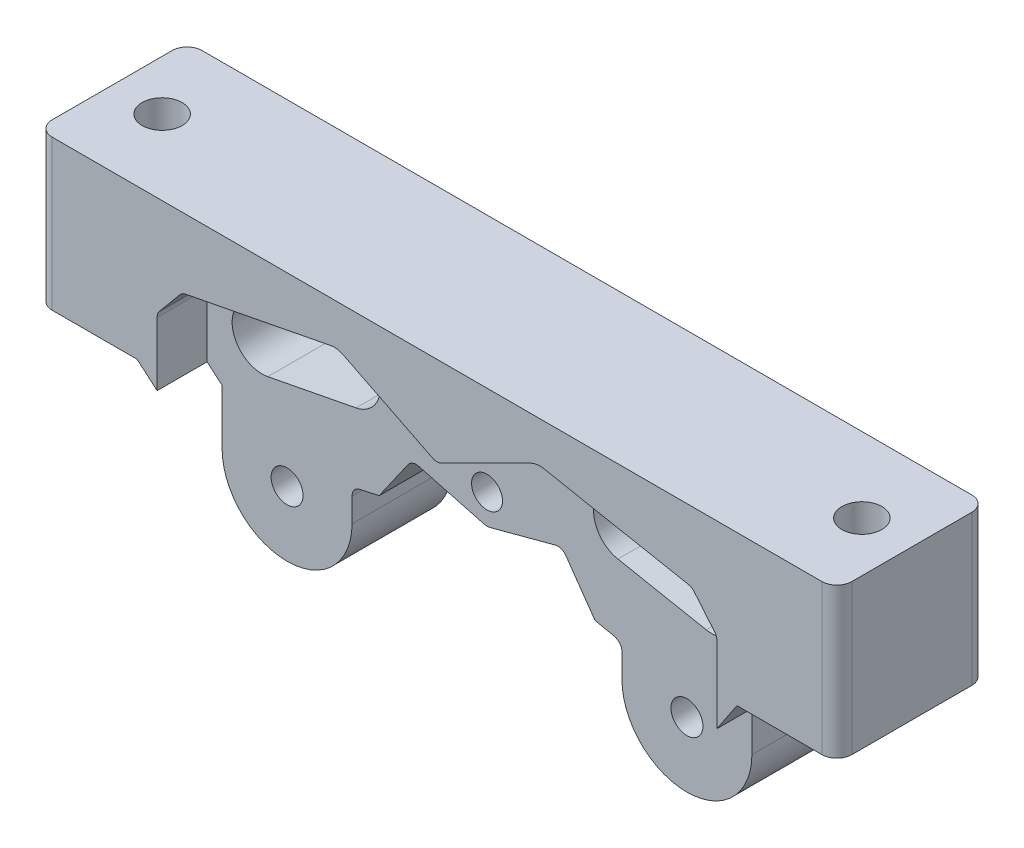
SolidWorks part; units mm, degrees
ref_plane "Front Plane" through (0, 0, 0) normal (0, 0, 1) x (1, 0, 0)
ref_plane "Top Plane" through (0, 0, 0) normal (0, 1, 0) x (1, 0, 0)
ref_plane "Right Plane" through (0, 0, 0) normal (1, 0, 0) x (0, 0, -1)
sketch "Sketch1" plane through (0, 0, 0) normal (0, 0, 1) x (1, 0, 0)
  line L0 (78, 15) -> (78, 0) construction
  line L1 (0, 0) -> (48, 0)
  line L2 (0, 0) -> (0, 15)
  line L3 (0, 15) -> (156, 15)
  line L4 (156, 0) -> (156, 15)
  line L5 (78, 0) -> (78, -15) construction
  line L6 (108, 0) -> (156, 0)
  line L8 (48, 0) -> (48, -15)
  line L9 (48, -15) -> (108, -15)
  line L10 (108, 0) -> (108, -15)
  point P13 (78, -15)
  dimension "D1" = 156
  dimension "D2" = 15
  dimension "D3" = 30
  dimension "D4" = 60
extrude "Boss-Extrude1" add sketch "Sketch1" along normal blind 15
sketch "Sketch2" plane through (0, 0, 15) normal (0, 0, 1) x (1, 0, 0)
  line L0 (78, -15) -> (78, 15) construction
  line L1 (48, -15) -> (108, -15) construction
  line L2 (156, 15) -> (0, 15) construction
  line L3 (85.5, -2) -> (70.5, -2) construction
  line L4 (0, 15) -> (0, 0) construction
  line L5 (0, 7.5) -> (156, 7.5) construction
  line L6 (156, 0) -> (156, 15) construction
  line L7 (89, -5) -> (67, -5) construction
  line L8 (108, 0) -> (48, 0) construction
  line L9 (67.633, 6) -> (88.367, 6) construction
  line L10 (108, -15) -> (108, 0) construction
  line L11 (108, -7.5) -> (48, -7.5) construction
  line L12 (48, 0) -> (48, -15) construction
  line L13 (68, 11) -> (88, 11) construction
  line L14 (77.5528, 6.2236) -> (68.6076, 10.6962)
  line L15 (78.4472, 6.2236) -> (87.3924, 10.6962)
  line L16 (50, 5) -> (106, 5) construction
  line L17 (52.5, 8) -> (103.5, 8) construction
  line L18 (88.6669, 10.8709) -> (103.15, 8.0677)
  line L20 (52.85, 8.0677) -> (67.3331, 10.8709)
  line L21 (105.7682, 5.2781) -> (103.7282, 7.7261)
  line L22 (52.2718, 7.7261) -> (50.2318, 5.2781)
  line L23 (50, 4.638) -> (50, -15)
  line L24 (50, -15) -> (106, -15)
  line L25 (106, -15) -> (106, 4.638)
  arc A0 (78.4472, 6.2236) -> (77.5528, 6.2236) centre (78, 7.118) cw
  arc A1 (67.3331, 10.8709) -> (68.6076, 10.6962) centre (67.7131, 8.9074) cw
  arc A2 (87.3924, 10.6962) -> (88.6669, 10.8709) centre (88.2869, 8.9074) cw
  arc A3 (103.7282, 7.7261) -> (103.15, 8.0677) centre (102.96, 7.086) ccw
  arc A4 (106, 4.638) -> (105.7682, 5.2781) centre (105, 4.638) ccw
  arc A5 (52.2718, 7.7261) -> (52.85, 8.0677) centre (53.04, 7.086) cw
  arc A6 (50, 4.638) -> (50.2318, 5.2781) centre (51, 4.638) cw
  point P24 (78, -2)
  point P27 (78, -5)
  point P30 (78, 6)
  point P33 (78, 11)
  point P37 (78, 5)
  point P40 (78, 8)
  point P45 (78, 6)
  dimension "D10" = 1
  dimension "D11" = 2
  dimension "D12" = 2
  dimension "D13" = 1
  dimension "D14" = 1
  dimension "D15" = 1
  dimension "D16" = 1
  dimension "D17" = 15
  dimension "D1" = 17
  dimension "D2" = 9
  dimension "D3" = 20
  dimension "D4" = 4
  dimension "D5" = 20
  dimension "D6" = 56
  dimension "D7" = 10
  dimension "D8" = 7
  dimension "D9" = 51
  dimension "D18" = 22
sketch "Sketch3" plane through (0, 0, 15) normal (0, 0, 1) x (1, 0, 0)
  line L0 (78, -15) -> (78, 15) construction
  line L1 (156, 15) -> (0, 15) construction
  circle A0 centre (78, 1) radius 1.55
  dimension "D2" = 3.1
  dimension "D1" = 14
sketch "Sketch4" plane through (0, 0, 15) normal (0, 0, 1) x (1, 0, 0)
  line L1 (78, -15) -> (78, 15) construction
  line L5 (156, 15) -> (0, 15) construction
  line L7 (78.2577, -1.9313) -> (78, -1.9609)
  line L15 (68.5726, -15) -> (87.4274, -15)
  line L16 (108, 0) -> (48, 0) construction
  line L17 (70.0989, -0.573) -> (67.2009, -4.7129)
  line L18 (71.1758, -0.1802) -> (77.7423, -1.9313)
  line L19 (85.5, -2) -> (70.5, -2) construction
  line L22 (84.8242, -0.1802) -> (78.2577, -1.9313)
  line L23 (85.9011, -0.573) -> (88.7991, -4.7129)
  line L24 (67.5746, -14.0633) -> (67.0222, -5.3497)
  line L25 (88.9778, -5.3497) -> (88.4254, -14.0633)
  line L26 (78, -1.9609) -> (77.7423, -1.9313)
  arc A0 (70.0989, -0.573) -> (71.1758, -0.1802) centre (70.9181, -1.1464) cw
  arc A2 (85.9011, -0.573) -> (84.8242, -0.1802) centre (85.0819, -1.1464) ccw
  arc A3 (67.0222, -5.3497) -> (67.2009, -4.7129) centre (68.0202, -5.2864) cw
  arc A4 (88.9778, -5.3497) -> (88.7991, -4.7129) centre (87.9798, -5.2864) ccw
  arc A5 (88.4254, -14.0633) -> (87.4274, -15) centre (87.4274, -14) cw
  arc A6 (68.5726, -15) -> (67.5746, -14.0633) centre (68.5726, -14) cw
  point P9 (78, -15)
  point P18 (70.5, 0)
  point P21 (78, -2)
  point P24 (85.5, 0)
  point P27 (67, -5)
  point P30 (89, -5)
  dimension "D1" = 1
  dimension "D3" = 1
  dimension "D4" = 1
  dimension "D5" = 1
  dimension "D7" = 1
  dimension "D8" = 1
  dimension "D6" = 30
extrude "Cut-Extrude7" cut sketch "Sketch2" against normal blind 5
extrude "Cut-Extrude8" cut sketch "Sketch4" against normal blind 35
extrude "Cut-Extrude10" cut sketch "Sketch3" against normal blind 32
sketch "Sketch10" plane through (0, 0, 10) normal (0, 0, 1) x (1, 0, 0)
  line L0 (88.6669, 10.8709) -> (103.15, 8.0677) construction
  line L1 (103.15, 8.0677) -> (52.85, 8.0677) construction
  line L2 (52.85, 8.0677) -> (67.3331, 10.8709) construction
  line L3 (55.5, 2.9786) -> (65.3178, 4.8788) construction
  line L4 (50, 4.638) -> (50, -15) construction
  line L5 (54.9299, 5.9239) -> (63.766, 7.6341)
  line L6 (78, 15) -> (78, -15.0706) construction
  line L7 (156, 15) -> (0, 15) construction
  line L8 (56.0701, 0.0332) -> (64.9061, 1.7434)
  line L9 (101.0701, 5.9239) -> (92.234, 7.6341)
  line L10 (99.9299, 0.0332) -> (91.0939, 1.7434)
  line L11 (58, -8.5) -> (98, -8.5) construction
  circle A0 centre (55.5, 2.9786) radius 1.5 construction
  circle A1 centre (58.4453, 3.5486) radius 1.5 construction
  circle A2 centre (61.3907, 4.1187) radius 1.5 construction
  circle A3 centre (64.336, 4.6888) radius 1.5 construction
  circle A4 centre (100.5, 2.9786) radius 1.5 construction
  circle A5 centre (97.5547, 3.5486) radius 1.5 construction
  circle A6 centre (94.6093, 4.1187) radius 1.5 construction
  circle A7 centre (91.664, 4.6888) radius 1.5 construction
  arc A8 (54.9299, 5.9239) -> (56.0701, 0.0332) centre (55.5, 2.9786) ccw
  arc A9 (64.9061, 1.7434) -> (63.766, 7.6341) centre (64.336, 4.6888) ccw
  arc A10 (58.3532, 2.0515) -> (57.8012, 4.9033) centre (55.5, 2.9786) ccw
  arc A11 (61.4829, 5.6159) -> (62.0348, 2.7641) centre (64.336, 4.6888) ccw
  arc A12 (101.0701, 5.9239) -> (99.9299, 0.0332) centre (100.5, 2.9786) cw
  arc A13 (91.0939, 1.7434) -> (92.234, 7.6341) centre (91.664, 4.6888) cw
  circle A14 centre (98, -8.5) radius 1.6
  circle A15 centre (58, -8.5) radius 1.6
  point P45 (78, -8.5)
  dimension "D5" = 3
  dimension "D6" = 3
  dimension "D7" = 3
  dimension "D8" = 3
  dimension "D9" = 6
  dimension "D10" = 6
  dimension "D13" = 3.2
  dimension "D1" = 5.5
  dimension "D2" = 5.5
  dimension "D3" = 10
  dimension "D4" = 5.5
  dimension "D11" = 40
  dimension "D12" = 23.5
extrude "Cut-Extrude11" cut sketch "Sketch10" against normal blind 32
sketch "Sketch11" plane through (0, 0, 0) normal (0, 0, -1) x (-1, 0, 0)
  circle A0 centre (-58, -8.5) radius 4.1
  circle A2 centre (-98, -8.5) radius 4.1
  dimension "D1" = 8.2
  dimension "D2" = 8.2
extrude "Cut-Extrude12" cut sketch "Sketch11" against normal blind 0.4
sketch "Sketch13" plane through (0, 0, 0) normal (0, 0, -1) x (-1, 0, 0)
  line L0 (-78, 15) -> (-78, -15.0108) construction
  line L3 (-156, 15) -> (0, 15) construction
  line L4 (-78, -15.0108) -> (-108, -15) construction
  line L7 (-108, -15) -> (-108, 0) construction
  line L8 (-108, 0) -> (-48, 0) construction
  line L9 (-48, 0) -> (-48, -15) construction
  line L10 (-48, -15) -> (-78, -15.0108) construction
  line L11 (-78, -15.0108) -> (-87.9798, -5.2864) construction
  line L12 (-87.9798, -5.2864) -> (-68.0202, -5.2864) construction
  line L13 (-68.0202, -5.2864) -> (-78, -15.0108) construction
  line L14 (-78, -15.0108) -> (-98, -8.5) construction
  line L15 (-98, -8.5) -> (-108, -8.5) construction
  line L16 (-78, -15.0108) -> (-58, -8.5) construction
  line L17 (-58, -8.5) -> (-48, -8.5) construction
  line L18 (-91.5, -8.5) -> (-91.5, -6.0964)
  line L19 (-104.5, -8.5) -> (-104.5, -4)
  line L21 (-90.7077, -5.1182) -> (-88.7991, -4.7129)
  line L22 (-108, 0) -> (-108, -15)
  line L23 (-108, -15) -> (-87.4274, -15)
  line L24 (-87.4274, -15) -> (-88.7991, -4.7129)
  line L25 (-58, -8.5) -> (-48, -8.5) construction
  line L26 (-48, -15) -> (-48, 0) construction
  line L27 (-68.5726, -15) -> (-67.2009, -4.7129)
  line L28 (-48, -15) -> (-68.5726, -15)
  line L29 (-48, 0) -> (-48, -15)
  line L30 (-65.2923, -5.1182) -> (-67.2009, -4.7129)
  line L31 (-51.5, -3) -> (-48, 0)
  line L32 (-51.5, -8.5) -> (-51.5, -3)
  line L33 (-64.5, -8.5) -> (-64.5, -6.0964)
  line L34 (-105.5, -3) -> (-106, -3)
  line L35 (-106, -15) -> (-106, 4.638) construction
  line L36 (-106, -3) -> (-108, 0)
  circle A0 centre (-98, -8.5) radius 6.5 construction
  arc A2 (-91.5, -6.0964) -> (-90.7077, -5.1182) centre (-90.5, -6.0964) cw
  arc A3 (-104.5, -8.5) -> (-91.5, -8.5) centre (-98, -8.5) ccw
  circle A4 centre (-58, -8.5) radius 6.5 construction
  arc A5 (-64.5, -6.0964) -> (-65.2923, -5.1182) centre (-65.5, -6.0964) ccw
  arc A6 (-51.5, -8.5) -> (-64.5, -8.5) centre (-58, -8.5) cw
  arc A7 (-104.5, -4) -> (-105.5, -3) centre (-105.5, -4) ccw
  point P51 (-104.5, -3)
  dimension "D3" = 1
  dimension "D4" = 1
  dimension "D1" = 3
  dimension "D2" = 3.5
extrude "Cut-Extrude13" cut sketch "Sketch13" against normal blind 32
sketch "Sketch14" plane through (0, 15, 0) normal (0, 1, 0) x (1, 0, 0)
  line L0 (156, -7.5) -> (0, -7.5) construction
  line L1 (156, 0) -> (0, 0) construction
  line L2 (156, 0) -> (156, -15) construction
  line L3 (156, -15) -> (0, -15) construction
  line L4 (0, 0) -> (0, -15) construction
  line L6 (78, 0) -> (78, -15) construction
  circle A0 centre (113, -7.5) radius 2
  circle A1 centre (43, -7.5) radius 2
  dimension "D1" = 4
  dimension "66" = 70
extrude "Cut-Extrude14" cut sketch "Sketch14" against normal blind 22
sketch "Sketch15" plane through (0, 0, 0) normal (0, -1, 0) x (1, 0, 0)
  line L1 (117.0415, 7.5) -> (115.0207, 11)
  line L2 (115.0207, 11) -> (110.9793, 11)
  line L3 (110.9793, 11) -> (108.9585, 7.5)
  line L4 (108.9585, 7.5) -> (110.9793, 4)
  line L5 (110.9793, 4) -> (115.0207, 4)
  line L6 (115.0207, 4) -> (117.0415, 7.5)
  line L7 (38.9585, 7.5) -> (40.9793, 4)
  line L8 (40.9793, 4) -> (45.0207, 4)
  line L9 (45.0207, 4) -> (47.0415, 7.5)
  line L10 (47.0415, 7.5) -> (45.0207, 11)
  line L11 (45.0207, 11) -> (40.9793, 11)
  line L12 (40.9793, 11) -> (38.9585, 7.5)
  circle A0 centre (113, 7.5) radius 3.5 construction
  circle A1 centre (43, 7.5) radius 3.5 construction
  point P10 (113, 11)
  dimension "D1" = 7
  dimension "D2" = 7
extrude "Cut-Extrude15" cut sketch "Sketch15" against normal blind 3
sketch "Sketch16" plane through (0, 15, 0) normal (0, 1, 0) x (1, 0, 0)
  line L0 (156, -7.5) -> (0, -7.5) construction
  line L1 (156, -15) -> (0, -15) construction
  line L2 (156, -15) -> (156, 0) construction
  line L3 (156, 0) -> (0, 0) construction
  line L4 (0, -15) -> (0, 0) construction
  line L5 (78, -15) -> (78, 0) construction
  line L6 (118, -15) -> (156, -15)
  line L7 (156, 0) -> (156, -15)
  line L8 (118, -15) -> (38, -15) construction
  line L9 (118, -15) -> (118, 0) construction
  line L10 (118, 0) -> (38, 0) construction
  line L11 (38, -15) -> (38, 0) construction
  line L12 (38, 0) -> (0, 0)
  line L13 (38, 0) -> (38, -15)
  line L14 (38, -15) -> (0, -15)
  line L15 (0, 0) -> (0, -15)
  line L16 (118, 0) -> (156, 0)
  line L17 (118, 0) -> (118, -15)
  dimension "D1" = 80
extrude "Cut-Extrude16" cut sketch "Sketch16" against normal blind 20
sketch "Sketch17" plane through (0, 15, 0) normal (0, 1, 0) x (1, 0, 0)
  line L0 (118, -13.5) -> (118, -15)
  line L1 (116.5, 0) -> (39.5, 0) construction
  line L2 (118, -1.5) -> (118, -13.5) construction
  line L3 (116.5, -15) -> (39.5, -15) construction
  line L4 (38, -1.5) -> (38, -13.5) construction
  line L5 (118, -15) -> (116.5, -15)
  line L6 (116.5, 0) -> (118, 0)
  line L7 (118, 0) -> (118, -1.5)
  line L8 (39.5, 0) -> (38, 0)
  line L9 (38, 0) -> (38, -1.5)
  line L10 (39.5, -15) -> (38, -15)
  line L11 (38, -15) -> (38, -13.5)
  arc A0 (38, -13.5) -> (39.5, -15) centre (39.5, -13.5) ccw
  arc A1 (38, -1.5) -> (39.5, 0) centre (39.5, -1.5) cw
  arc A2 (116.5, 0) -> (118, -1.5) centre (116.5, -1.5) cw
  arc A3 (118, -13.5) -> (116.5, -15) centre (116.5, -13.5) cw
  point P8 (38, -15)
  point P13 (118, 0)
  dimension "D1" = 1.5
extrude "Cut-Extrude17" cut sketch "Sketch17" against normal blind 20
